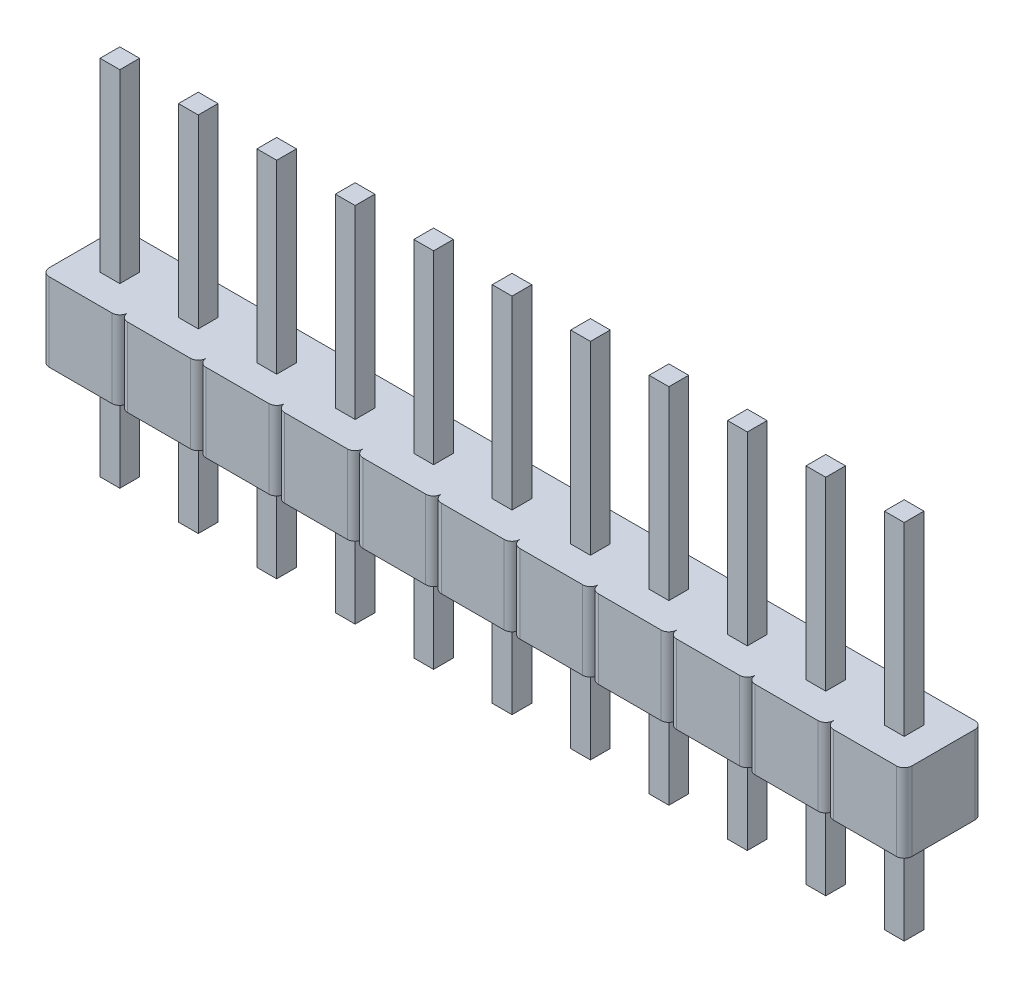
SolidWorks part; units mm, degrees
ref_plane "Front Plane" through (0, 0, 0) normal (0, 0, 1) x (1, 0, 0)
ref_plane "Top Plane" through (0, 0, 0) normal (0, 1, 0) x (1, 0, 0)
ref_plane "Right Plane" through (0, 0, 0) normal (1, 0, 0) x (0, 0, -1)
sketch "Sketch1" plane through (0, 0, 0) normal (0, 1, 0) x (1, 0, 0)
  line L0 (1.27, -1.016) -> (1.27, 1.016)
  line L1 (-1.016, -1.27) -> (1.016, -1.27)
  line L2 (-1.27, -1.016) -> (-1.27, 1.016)
  line L3 (-1.016, 1.27) -> (1.016, 1.27)
  line L4 (1.27, -1.016) -> (1.27, 1.016)
  line L5 (1.524, -1.27) -> (3.556, -1.27)
  line L6 (3.81, -1.016) -> (3.81, 1.016)
  line L7 (1.524, 1.27) -> (3.556, 1.27)
  line L8 (3.81, -1.016) -> (3.81, 1.016)
  line L9 (4.064, -1.27) -> (6.096, -1.27)
  line L10 (6.35, -1.016) -> (6.35, 1.016)
  line L11 (4.064, 1.27) -> (6.096, 1.27)
  line L12 (6.35, -1.016) -> (6.35, 1.016)
  line L13 (6.604, -1.27) -> (8.636, -1.27)
  line L14 (8.89, -1.016) -> (8.89, 1.016)
  line L15 (6.604, 1.27) -> (8.636, 1.27)
  line L16 (8.89, -1.016) -> (8.89, 1.016)
  line L17 (9.144, -1.27) -> (11.176, -1.27)
  line L18 (11.43, -1.016) -> (11.43, 1.016)
  line L19 (9.144, 1.27) -> (11.176, 1.27)
  line L20 (11.43, -1.016) -> (11.43, 1.016)
  line L21 (11.684, -1.27) -> (13.716, -1.27)
  line L22 (13.97, -1.016) -> (13.97, 1.016)
  line L23 (11.684, 1.27) -> (13.716, 1.27)
  line L24 (-3.81, -1.016) -> (-3.81, 1.016)
  line L25 (-3.556, -1.27) -> (-1.524, -1.27)
  line L26 (-1.27, -1.016) -> (-1.27, 1.016)
  line L27 (-3.556, 1.27) -> (-1.524, 1.27)
  line L28 (-6.35, -1.016) -> (-6.35, 1.016)
  line L29 (-6.096, -1.27) -> (-4.064, -1.27)
  line L30 (-3.81, -1.016) -> (-3.81, 1.016)
  line L31 (-6.096, 1.27) -> (-4.064, 1.27)
  line L32 (-8.89, -1.016) -> (-8.89, 1.016)
  line L33 (-8.636, -1.27) -> (-6.604, -1.27)
  line L34 (-6.35, -1.016) -> (-6.35, 1.016)
  line L35 (-8.636, 1.27) -> (-6.604, 1.27)
  line L36 (-11.43, -1.016) -> (-11.43, 1.016)
  line L37 (-11.176, -1.27) -> (-9.144, -1.27)
  line L38 (-8.89, -1.016) -> (-8.89, 1.016)
  line L39 (-11.176, 1.27) -> (-9.144, 1.27)
  line L40 (-13.97, -1.016) -> (-13.97, 1.016)
  line L41 (-13.716, -1.27) -> (-11.684, -1.27)
  line L42 (-11.43, -1.016) -> (-11.43, 1.016)
  line L43 (-13.716, 1.27) -> (-11.684, 1.27)
  arc A0 (-1.016, 1.27) -> (-1.27, 1.016) centre (-1.016, 1.016) ccw
  arc A1 (1.27, -1.016) -> (1.016, -1.27) centre (1.016, -1.016) cw
  arc A2 (-1.27, -1.016) -> (-1.016, -1.27) centre (-1.016, -1.016) ccw
  arc A3 (1.27, 1.016) -> (1.016, 1.27) centre (1.016, 1.016) ccw
  arc A4 (1.27, -1.016) -> (1.524, -1.27) centre (1.524, -1.016) ccw
  arc A5 (1.524, 1.27) -> (1.27, 1.016) centre (1.524, 1.016) ccw
  arc A6 (3.81, -1.016) -> (3.556, -1.27) centre (3.556, -1.016) cw
  arc A7 (3.81, 1.016) -> (3.556, 1.27) centre (3.556, 1.016) ccw
  arc A8 (3.81, -1.016) -> (4.064, -1.27) centre (4.064, -1.016) ccw
  arc A9 (4.064, 1.27) -> (3.81, 1.016) centre (4.064, 1.016) ccw
  arc A10 (6.35, -1.016) -> (6.096, -1.27) centre (6.096, -1.016) cw
  arc A11 (6.35, 1.016) -> (6.096, 1.27) centre (6.096, 1.016) ccw
  arc A12 (6.35, -1.016) -> (6.604, -1.27) centre (6.604, -1.016) ccw
  arc A13 (6.604, 1.27) -> (6.35, 1.016) centre (6.604, 1.016) ccw
  arc A14 (8.89, -1.016) -> (8.636, -1.27) centre (8.636, -1.016) cw
  arc A15 (8.89, 1.016) -> (8.636, 1.27) centre (8.636, 1.016) ccw
  arc A16 (8.89, -1.016) -> (9.144, -1.27) centre (9.144, -1.016) ccw
  arc A17 (9.144, 1.27) -> (8.89, 1.016) centre (9.144, 1.016) ccw
  arc A18 (11.43, -1.016) -> (11.176, -1.27) centre (11.176, -1.016) cw
  arc A19 (11.43, 1.016) -> (11.176, 1.27) centre (11.176, 1.016) ccw
  arc A20 (11.43, -1.016) -> (11.684, -1.27) centre (11.684, -1.016) ccw
  arc A21 (11.684, 1.27) -> (11.43, 1.016) centre (11.684, 1.016) ccw
  arc A22 (13.97, -1.016) -> (13.716, -1.27) centre (13.716, -1.016) cw
  arc A23 (13.97, 1.016) -> (13.716, 1.27) centre (13.716, 1.016) ccw
  arc A24 (-3.81, -1.016) -> (-3.556, -1.27) centre (-3.556, -1.016) ccw
  arc A25 (-3.556, 1.27) -> (-3.81, 1.016) centre (-3.556, 1.016) ccw
  arc A26 (-1.27, -1.016) -> (-1.524, -1.27) centre (-1.524, -1.016) cw
  arc A27 (-1.27, 1.016) -> (-1.524, 1.27) centre (-1.524, 1.016) ccw
  arc A28 (-6.35, -1.016) -> (-6.096, -1.27) centre (-6.096, -1.016) ccw
  arc A29 (-6.096, 1.27) -> (-6.35, 1.016) centre (-6.096, 1.016) ccw
  arc A30 (-3.81, -1.016) -> (-4.064, -1.27) centre (-4.064, -1.016) cw
  arc A31 (-3.81, 1.016) -> (-4.064, 1.27) centre (-4.064, 1.016) ccw
  arc A32 (-8.89, -1.016) -> (-8.636, -1.27) centre (-8.636, -1.016) ccw
  arc A33 (-8.636, 1.27) -> (-8.89, 1.016) centre (-8.636, 1.016) ccw
  arc A34 (-6.35, -1.016) -> (-6.604, -1.27) centre (-6.604, -1.016) cw
  arc A35 (-6.35, 1.016) -> (-6.604, 1.27) centre (-6.604, 1.016) ccw
  arc A36 (-11.43, -1.016) -> (-11.176, -1.27) centre (-11.176, -1.016) ccw
  arc A37 (-11.176, 1.27) -> (-11.43, 1.016) centre (-11.176, 1.016) ccw
  arc A38 (-8.89, -1.016) -> (-9.144, -1.27) centre (-9.144, -1.016) cw
  arc A39 (-8.89, 1.016) -> (-9.144, 1.27) centre (-9.144, 1.016) ccw
  arc A40 (-13.97, -1.016) -> (-13.716, -1.27) centre (-13.716, -1.016) ccw
  arc A41 (-13.716, 1.27) -> (-13.97, 1.016) centre (-13.716, 1.016) ccw
  arc A42 (-11.43, -1.016) -> (-11.684, -1.27) centre (-11.684, -1.016) cw
  arc A43 (-11.43, 1.016) -> (-11.684, 1.27) centre (-11.684, 1.016) ccw
  point P0 (0, 0)
  point P6 (0, 1.27)
  point P8 (1.27, 0)
  point P11 (-1.27, 1.27)
  point P18 (1.27, 1.27)
  dimension "D2" = 0.254
  dimension "D1" = 2.54
  dimension "D5" = 13.97
  dimension "D6" = 13.97
  dimension "D3" = 6
  dimension "D4" = 6
extrude "Boss-Extrude1" add sketch "Sketch1" along normal blind 2.54 contours L36 A43 L43 A41 L40 A40 L41 A42 | L32 A39 L39 A37 L36 A36 L37 A38 | L28 A35 L35 A33 L32 A32 L33 A34 | L24 A31 L31 A29 L28 A28 L29 A30 | L2 A27 L27 A25 L24 A24 L25 A26 | L0 A3 L3 A0 L2 A2 L1 A1 | L6 A7 L7 A5 L0 A4 L5 A6 | L10 A11 L11 A9 L6 A8 L9 A10 | L14 A15 L15 A13 L10 A12 L13 A14 | L18 A19 L19 A17 L14 A16 L17 A18 | L22 A23 L23 A21 L18 A20 L21 A22
sketch "Sketch2" plane through (0, 2.54, 0) normal (0, 1, 0) x (1, 0, 0)
  line L0 (-13.716, 1.27) -> (-11.684, 1.27) construction
  line L5 (-13.02, -0.32) -> (-12.38, -0.32)
  line L6 (-13.02, -0.32) -> (-13.02, 0.32)
  line L7 (-13.02, 0.32) -> (-12.38, 0.32)
  line L8 (-12.38, -0.32) -> (-12.38, 0.32)
  line L9 (-13.02, -0.32) -> (-12.38, 0.32) construction
  line L10 (-13.02, 0.32) -> (-12.38, -0.32) construction
  line L11 (-13.97, -1.016) -> (-13.97, 1.016) construction
  line L12 (-10.48, -0.32) -> (-10.48, 0.32)
  line L13 (-10.48, -0.32) -> (-9.84, -0.32)
  line L14 (-9.84, -0.32) -> (-9.84, 0.32)
  line L15 (-10.48, 0.32) -> (-9.84, 0.32)
  line L16 (-7.94, -0.32) -> (-7.94, 0.32)
  line L17 (-7.94, -0.32) -> (-7.3, -0.32)
  line L18 (-7.3, -0.32) -> (-7.3, 0.32)
  line L19 (-7.94, 0.32) -> (-7.3, 0.32)
  line L20 (-5.4, -0.32) -> (-5.4, 0.32)
  line L21 (-5.4, -0.32) -> (-4.76, -0.32)
  line L22 (-4.76, -0.32) -> (-4.76, 0.32)
  line L23 (-5.4, 0.32) -> (-4.76, 0.32)
  line L24 (-2.86, -0.32) -> (-2.86, 0.32)
  line L25 (-2.86, -0.32) -> (-2.22, -0.32)
  line L26 (-2.22, -0.32) -> (-2.22, 0.32)
  line L27 (-2.86, 0.32) -> (-2.22, 0.32)
  line L28 (-0.32, -0.32) -> (-0.32, 0.32)
  line L29 (-0.32, -0.32) -> (0.32, -0.32)
  line L30 (0.32, -0.32) -> (0.32, 0.32)
  line L31 (-0.32, 0.32) -> (0.32, 0.32)
  line L32 (2.22, -0.32) -> (2.22, 0.32)
  line L33 (2.22, -0.32) -> (2.86, -0.32)
  line L34 (2.86, -0.32) -> (2.86, 0.32)
  line L35 (2.22, 0.32) -> (2.86, 0.32)
  line L36 (4.76, -0.32) -> (4.76, 0.32)
  line L37 (4.76, -0.32) -> (5.4, -0.32)
  line L38 (5.4, -0.32) -> (5.4, 0.32)
  line L39 (4.76, 0.32) -> (5.4, 0.32)
  line L40 (7.3, -0.32) -> (7.3, 0.32)
  line L41 (7.3, -0.32) -> (7.94, -0.32)
  line L42 (7.94, -0.32) -> (7.94, 0.32)
  line L43 (7.3, 0.32) -> (7.94, 0.32)
  line L44 (9.84, -0.32) -> (9.84, 0.32)
  line L45 (9.84, -0.32) -> (10.48, -0.32)
  line L46 (10.48, -0.32) -> (10.48, 0.32)
  line L47 (9.84, 0.32) -> (10.48, 0.32)
  line L48 (12.38, -0.32) -> (12.38, 0.32)
  line L49 (12.38, -0.32) -> (13.02, -0.32)
  line L50 (13.02, -0.32) -> (13.02, 0.32)
  line L51 (12.38, 0.32) -> (13.02, 0.32)
  point P0 (-12.7, 0)
  point P6 (12.7, 0.32)
  point P9 (-12.7, 1.27)
  point P12 (-13.97, 0)
  dimension "D1" = 0.64
  dimension "D3" = 25.4
  dimension "D2" = 11
extrude "Boss-Extrude2" add sketch "Sketch2" along normal blind 6 and the other way blind 5.74
